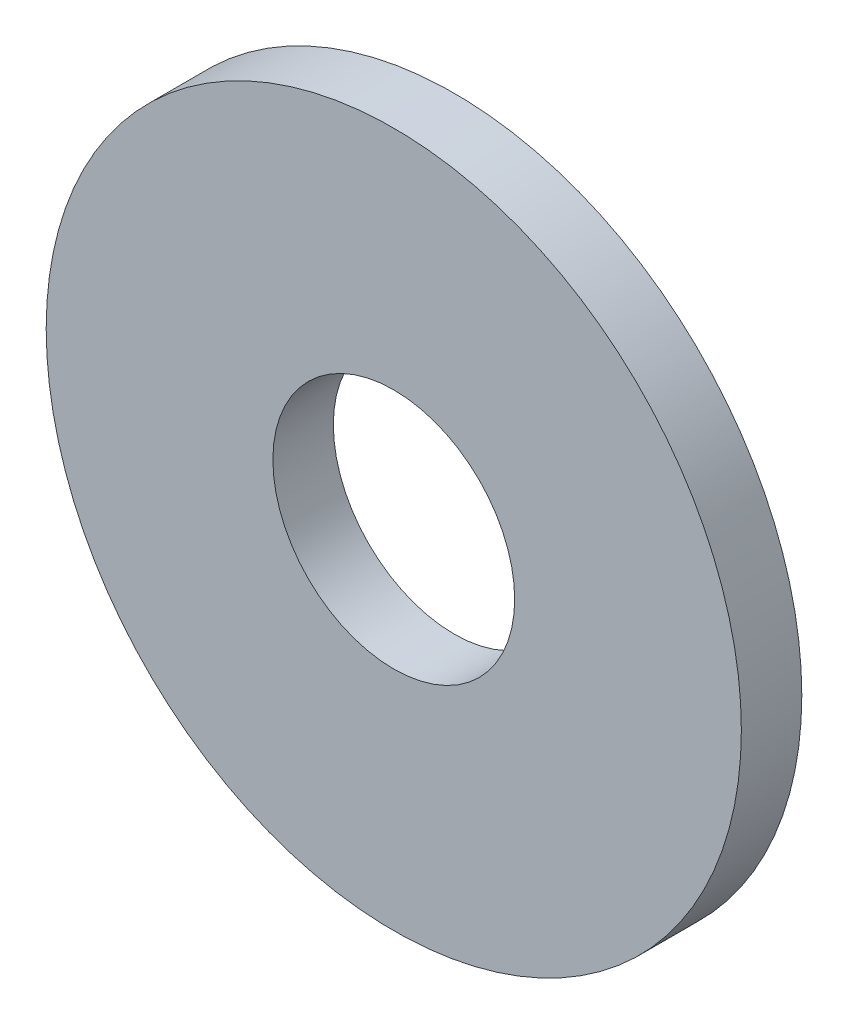
SolidWorks part; units mm, degrees
ref_plane "Front Plane" through (0, 0, 0) normal (0, 0, 1) x (1, 0, 0)
ref_plane "Top Plane" through (0, 0, 0) normal (0, 1, 0) x (1, 0, 0)
ref_plane "Right Plane" through (0, 0, 0) normal (1, 0, 0) x (0, 0, -1)
sketch "Sketch1" plane through (0, 0, 0) normal (0, 0, 1) x (1, 0, 0)
  circle A0 centre (0, 0) radius 4
  circle A1 centre (0, 0) radius 11.5
  dimension "D1" = 8
  dimension "D2" = 23
extrude "Boss-Extrude1" add sketch "Sketch1" along normal blind 2
